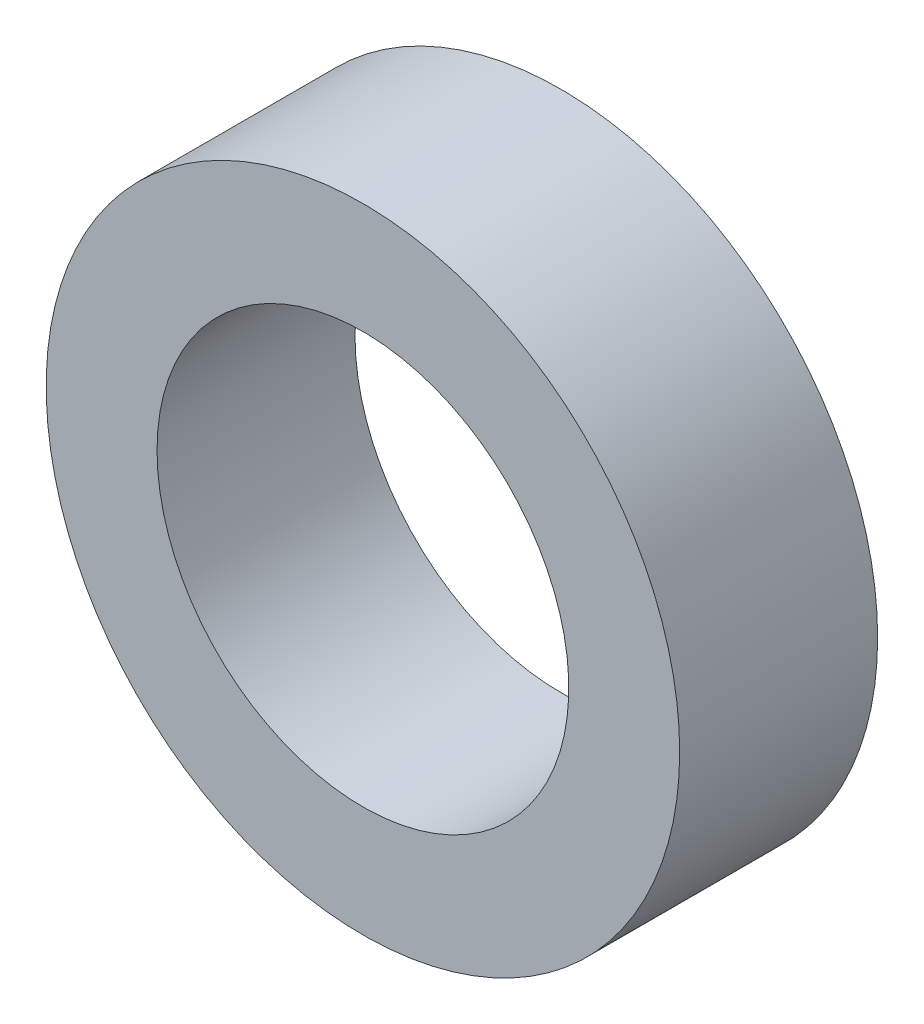
SolidWorks part; units mm, degrees
ref_plane "Front Plane" through (0, 0, 0) normal (0, 0, 1) x (1, 0, 0)
ref_plane "Top Plane" through (0, 0, 0) normal (0, 1, 0) x (1, 0, 0)
ref_plane "Right Plane" through (0, 0, 0) normal (1, 0, 0) x (0, 0, -1)
sketch "Sketch1" plane through (0, 0, 0) normal (0, 0, 1) x (1, 0, 0)
  circle A0 centre (0, 0) radius 5.08
extrude "Extrude1" add sketch "Sketch1" along normal blind 3.175
sketch "Sketch2" plane through (0, 0, 0) normal (0, 0, -1) x (-1, 0, 0)
  circle A0 centre (0, 0) radius 3.302
extrude "Cut-Extrude1" cut sketch "Sketch2" against normal through all
